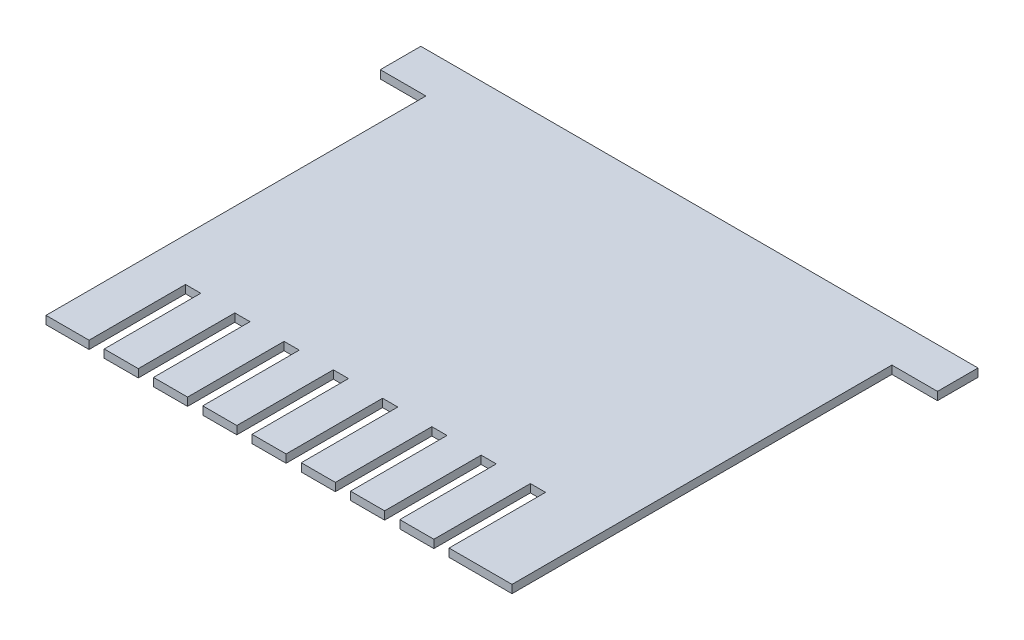
SolidWorks part; units mm, degrees
ref_plane "Front Plane" through (0, 0, 0) normal (0, 0, 1) x (1, 0, 0)
ref_plane "Top Plane" through (0, 0, 0) normal (0, 1, 0) x (1, 0, 0)
ref_plane "Right Plane" through (0, 0, 0) normal (1, 0, 0) x (0, 0, -1)
sketch "Sketch1" plane through (0, 0, 0) normal (0, 1, 0) x (1, 0, 0)
  line L0 (2.2, 75) -> (-6.8, 75)
  line L1 (2.2, 0) -> (94.2, 0) construction
  line L2 (-6.8, 83) -> (103.2, 83)
  line L3 (-6.8, 75) -> (-6.8, 83)
  line L4 (94.2, 75) -> (103.2, 75)
  line L5 (103.2, 75) -> (103.2, 83)
  line L7 (10.7, 0) -> (10.7, 19.05)
  line L8 (10.7, 19.05) -> (13.7, 19.05)
  line L9 (13.7, 19.05) -> (13.7, 0)
  line L10 (13.7, 0) -> (20.425, 0)
  line L11 (20.425, 0) -> (20.425, 19.05)
  line L12 (20.425, 19.05) -> (23.425, 19.05)
  line L13 (23.425, 19.05) -> (23.425, 0)
  line L14 (23.425, 0) -> (30.15, 0)
  line L15 (30.15, 0) -> (30.15, 19.05)
  line L16 (2.2, 0) -> (2.2, 75)
  line L17 (30.15, 19.05) -> (33.15, 19.05)
  line L18 (94.2, 0) -> (94.2, 75)
  line L19 (33.15, 19.05) -> (33.15, 0)
  line L20 (33.15, 0) -> (39.875, 0)
  line L21 (2.2, 0) -> (10.7, 0)
  line L22 (39.875, 0) -> (39.875, 19.05)
  line L23 (39.875, 19.05) -> (42.875, 19.05)
  line L24 (42.875, 19.05) -> (42.875, 0)
  line L25 (42.875, 0) -> (49.6, 0)
  line L26 (49.6, 0) -> (49.6, 19.05)
  line L27 (49.6, 19.05) -> (52.6, 19.05)
  line L28 (52.6, 19.05) -> (52.6, 0)
  line L29 (52.6, 0) -> (59.325, 0)
  line L30 (59.325, 0) -> (59.325, 19.05)
  line L31 (59.325, 19.05) -> (62.325, 19.05)
  line L32 (62.325, 19.05) -> (62.325, 0)
  line L33 (62.325, 0) -> (69.05, 0)
  line L34 (69.05, 0) -> (69.05, 19.05)
  line L35 (69.05, 19.05) -> (72.05, 19.05)
  line L36 (72.05, 19.05) -> (72.05, 0)
  line L37 (72.05, 0) -> (78.775, 0)
  line L38 (78.775, 0) -> (78.775, 19.05)
  line L39 (78.775, 19.05) -> (81.775, 19.05)
  line L40 (81.775, 19.05) -> (81.775, 0)
  line L41 (81.775, 0) -> (94.2, 0)
  point P11 (4.5, 95.6)
  dimension "D1" = 83
  dimension "D2" = 8
  dimension "D3" = 110
  dimension "D4" = 92
  dimension "D5" = 19.05
  dimension "D6" = 3
extrude "Boss-Extrude1" add sketch "Sketch1" along normal blind 1.6
ref_plane "center-of-slot" through (0, 0.8, 0) normal (0, 1, 0) x (1, 0, 0)
ref_plane "Plane1" [suppressed] through (50, 0, 0) normal (-1, 0, 0) x (0, 0, 1)
